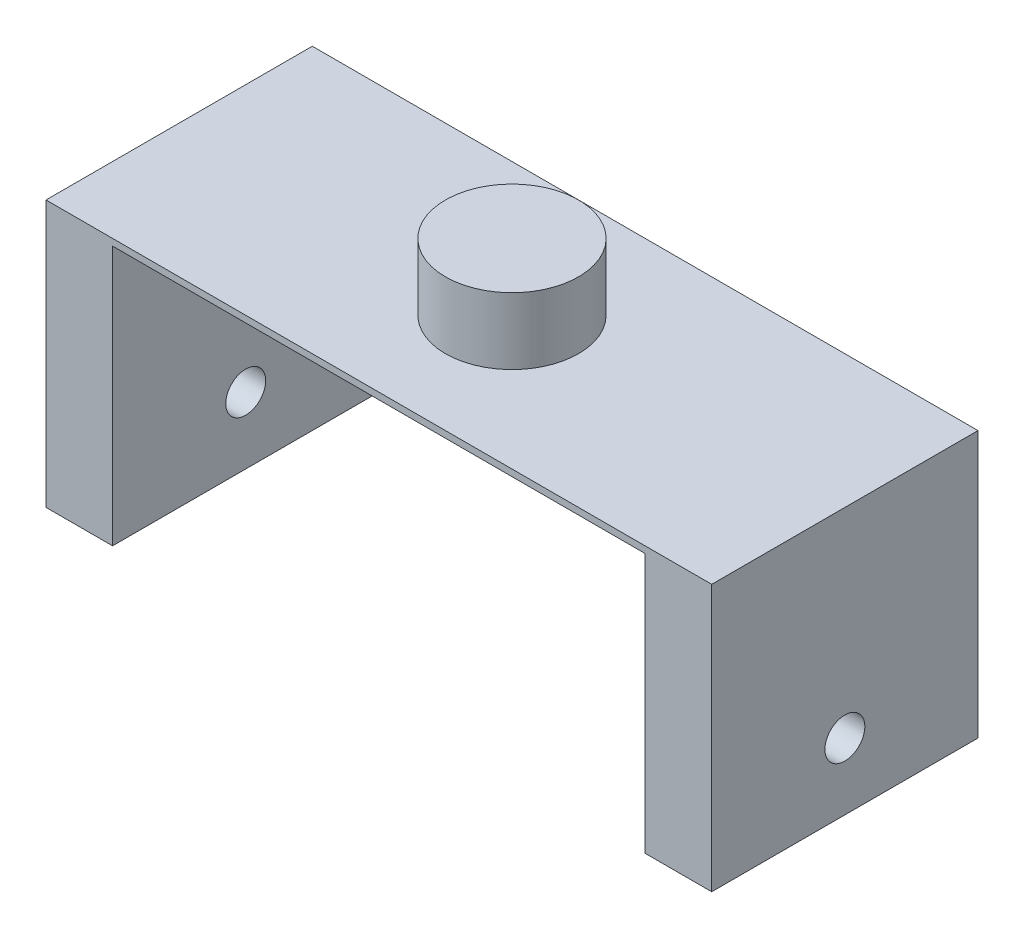
SolidWorks part; units mm, degrees
ref_plane "Front Plane" through (0, 0, 0) normal (0, 0, 1) x (1, 0, 0)
ref_plane "Top Plane" through (0, 0, 0) normal (0, 1, 0) x (1, 0, 0)
ref_plane "Right Plane" through (0, 0, 0) normal (1, 0, 0) x (0, 0, -1)
sketch "Sketch1" plane through (0, 0, 0) normal (0, 1, 0) x (1, 0, 0)
  line L1 (0, 0) -> (25.4, 0)
  line L2 (0, 0) -> (0, -10.16)
  line L3 (0, -10.16) -> (25.4, -10.16)
  line L4 (25.4, 0) -> (25.4, -10.16)
  dimension "D1" = 10.16
  dimension "D2" = 25.4
extrude "Boss-Extrude2" add sketch "Sketch1" along normal blind 0.254
sketch "Sketch2" plane through (0, 0.254, 0) normal (0, 1, 0) x (1, 0, 0)
  circle A0 centre (12.7, -5.08) radius 2.54
  dimension "D1" = 5.08
extrude "Boss-Extrude3" add sketch "Sketch2" along normal blind 2.54
sketch "Sketch3" plane through (0, 0.254, 0) normal (0, 1, 0) x (1, 0, 0)
  line L1 (0, 0) -> (2.54, 0)
  line L2 (0, 0) -> (0, -10.16)
  line L3 (0, -10.16) -> (2.54, -10.16)
  line L4 (2.54, 0) -> (2.54, -10.16)
  line L5 (25.4, 0) -> (22.86, 0)
  line L6 (25.4, 0) -> (25.4, -10.16)
  line L7 (25.4, -10.16) -> (22.86, -10.16)
  line L8 (22.86, 0) -> (22.86, -10.16)
  dimension "D1" = 2.54
  dimension "D2" = 2.54
  dimension "D3" = 10.16
  dimension "D4" = 10.16
extrude "Boss-Extrude4" add sketch "Sketch3" against normal blind 10.16
sketch "Sketch4" plane through (0, 0, 0) normal (-1, 0, 0) x (0, 0, 1)
  circle A0 centre (5.08, -7.366) radius 0.762
  dimension "D2" = 1.524
extrude "Cut-Extrude2" cut sketch "Sketch4" against normal blind 25.4
